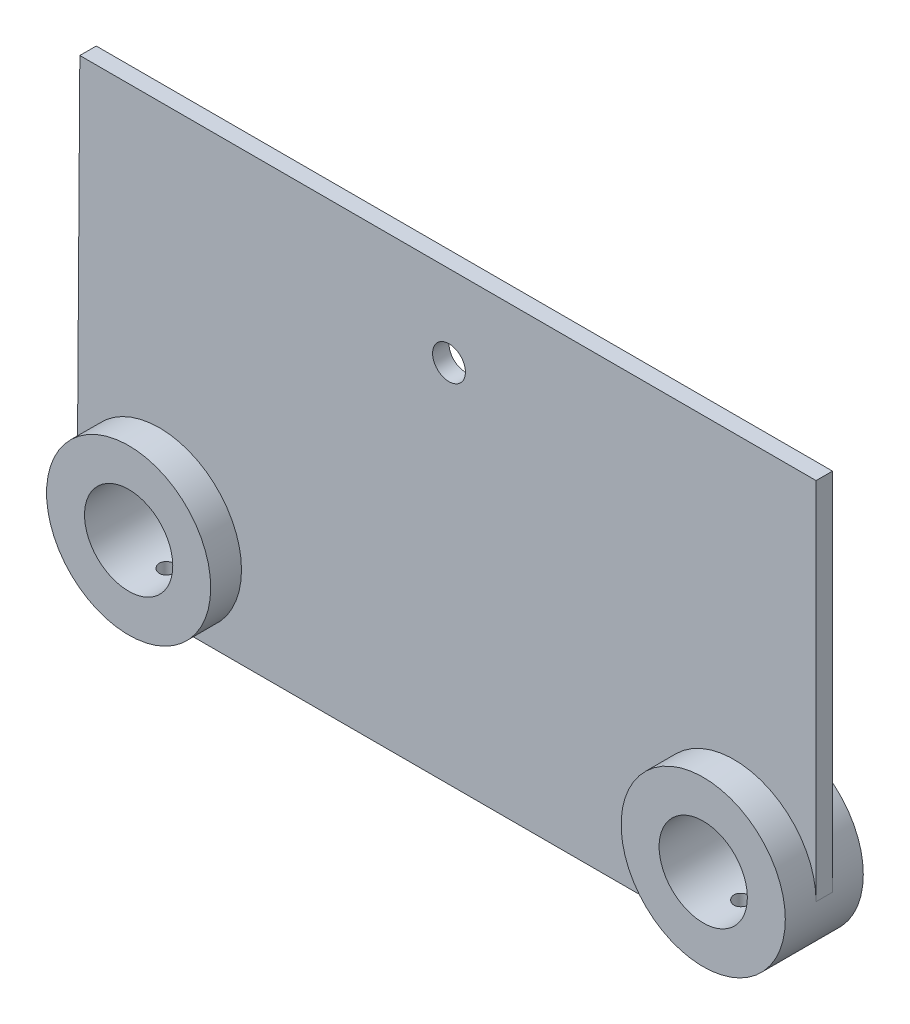
SolidWorks part; units mm, degrees
ref_plane "Front Plane" through (0, 0, 0) normal (0, 0, 1) x (1, 0, 0)
ref_plane "Top Plane" through (0, 0, 0) normal (0, 1, 0) x (1, 0, 0)
ref_plane "Right Plane" through (0, 0, 0) normal (1, 0, 0) x (0, 0, -1)
sketch "Sketch1" plane through (0, 0, 0) normal (0, 0, 1) x (1, 0, 0)
  line L0 (-70, -20) -> (70, -20)
  line L7 (-89.3895, 88.85) -> (-90, 0)
  line L8 (-89.3895, 88.85) -> (90, 88.85)
  line L10 (90, 88.85) -> (90, 0)
  circle A0 centre (70, 0) radius 10.75
  circle A1 centre (-70, 0) radius 10.75
  arc A3 (-90, 0) -> (-70, -20) centre (-70, 0) ccw
  arc A5 (70, -20) -> (90, 0) centre (70, 0) ccw
  dimension "D1" = 21.5
  dimension "D2" = 20
  dimension "D3" = 140
  dimension "D4" = 179.3895
  dimension "D5" = 88.85
extrude "Boss-Extrude1" add sketch "Sketch1" along normal mid plane 4
sketch "Sketch2" plane through (0, 0, 0) normal (0, 0, 1) x (1, 0, 0)
  line L0 (90, 88.85) -> (-89.3895, 88.85) construction
  circle A0 centre (0.5547, 69) radius 4
  dimension "D1" = 8
  dimension "D2" = 19.85
extrude "Cut-Extrude1" cut sketch "Sketch2" along normal up to surface and the other way up to surface up to face at (80.75, 0, 2) other way up to face at (0.1018, 21.5693, -2)
sketch "Sketch3" plane through (0, 0, 0) normal (0, 0, 1) x (1, 0, 0)
  circle A0 centre (-70, 0) radius 20
  circle A1 centre (-70, 0) radius 10.75 construction
  arc A2 (-90, 0) -> (-70, -20) centre (-70, 0) ccw construction
  circle A5 centre (-70, 0) radius 10.75
  circle A9 centre (70, 0) radius 20
  circle A10 centre (70, 0) radius 10.75
  circle A11 centre (70, 0) radius 10.75 construction
  dimension "D1" = 40
  dimension "D2" = 21.5
extrude "Boss-Extrude2" add sketch "Sketch3" along normal mid plane 19
sketch "Sketch6" plane through (0, 0, 0) normal (0, 1, 0) x (1, 0, 0)
  line L1 (70, -2) -> (70, 2) construction
  line L3 (-70, -2) -> (-70, 2) construction
  circle A0 centre (-70, 0) radius 2
  circle A1 centre (70, 0) radius 2
  point P11 (70, 0)
  point P13 (-70, 0)
  dimension "D1" = 4
  dimension "D2" = 140
extrude "Cut-Extrude2" cut sketch "Sketch6" against normal up to surface (20 mm away) up to face at (0, -20, 0)
